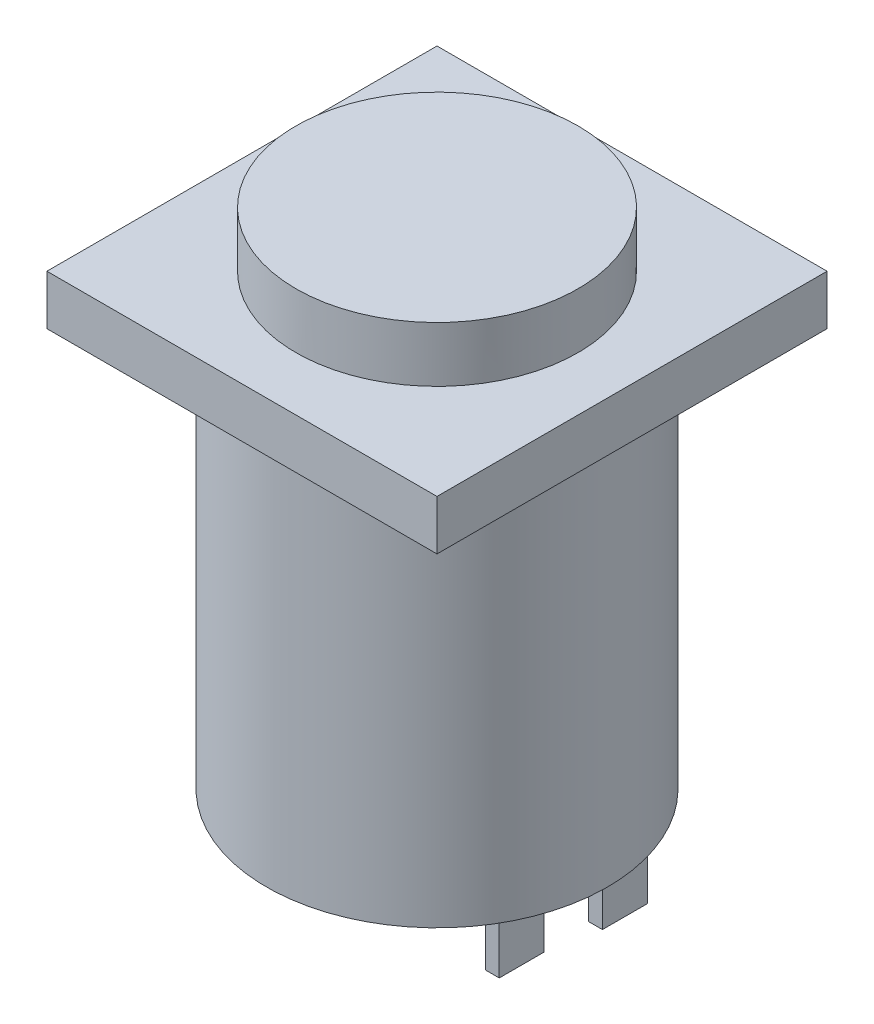
SolidWorks part; units mm, degrees
material "Delrin 2700 NC010, Low Viscosity Acetal Copolymer (SS)"
ref_plane "Front Plane" through (0, 0, 0) normal (0, 0, 1) x (1, 0, 0)
ref_plane "Top Plane" through (0, 0, 0) normal (0, 1, 0) x (1, 0, 0)
ref_plane "Right Plane" through (0, 0, 0) normal (1, 0, 0) x (0, 0, -1)
sketch "Sketch1" plane through (0, 0, 0) normal (0, 1, 0) x (1, 0, 0)
  line L0 (8.9535, -8.9535) -> (-8.9535, 8.9535) construction
  line L1 (8.9535, 8.9535) -> (-8.9535, 8.9535)
  line L2 (8.9535, 8.9535) -> (8.9535, -8.9535)
  line L3 (8.9535, -8.9535) -> (-8.9535, -8.9535)
  line L4 (-8.9535, 8.9535) -> (-8.9535, -8.9535)
  dimension "D1" = 17.907
extrude "Boss-Extrude1" add sketch "Sketch1" along normal blind 2.286
sketch "Sketch2" plane through (0, 2.286, 0) normal (0, 1, 0) x (1, 0, 0)
  circle A0 centre (0, 0) radius 6.477
  dimension "D1" = 12.954
extrude "Boss-Extrude2" add sketch "Sketch2" along normal blind 2.54
sketch "Sketch3" plane through (0, 0, 0) normal (0, -1, 0) x (1, 0, 0)
  circle A0 centre (0, 0) radius 7.8232
  dimension "D1" = 15.6464
extrude "Boss-Extrude3" add sketch "Sketch3" along normal blind 18.288
sketch "Sketch4" plane through (0, -18.288, 0) normal (0, -1, 0) x (1, 0, 0)
  line L0 (-2.2225, 0) -> (2.2225, 0) construction
  line L1 (-2.8575, 0) -> (-2.2225, 0)
  line L2 (-2.8575, 0) -> (-2.8575, -2.0574)
  line L3 (-2.8575, -2.0574) -> (-2.2225, -2.0574)
  line L4 (-2.2225, 0) -> (-2.2225, -2.0574)
  line L5 (2.2225, 0) -> (2.8575, 0)
  line L6 (2.2225, 0) -> (2.2225, -2.0574)
  line L7 (2.2225, -2.0574) -> (2.8575, -2.0574)
  line L8 (2.8575, 0) -> (2.8575, -2.0574)
  line L9 (-3.302, -4.2926) -> (-2.667, -4.2926)
  line L10 (-3.302, -4.2926) -> (-3.302, -6.35)
  line L11 (-3.302, -6.35) -> (-2.667, -6.35)
  line L12 (-2.667, -4.2926) -> (-2.667, -6.35)
  line L13 (3.302, -4.2926) -> (2.667, -4.2926)
  line L14 (3.302, -4.2926) -> (3.302, -6.35)
  line L15 (3.302, -6.35) -> (2.667, -6.35)
  line L16 (2.667, -4.2926) -> (2.667, -6.35)
  line L17 (-2.667, -4.2926) -> (2.667, -4.2926) construction
  line L18 (0, 0) -> (0, -4.2926) construction
  dimension "D1" = 2.0574
  dimension "D2" = 0.635
  dimension "D3" = 6.35
  dimension "D4" = 6.604
  dimension "D5" = 5.715
extrude "Boss-Extrude4" add sketch "Sketch4" along normal blind 6.096
